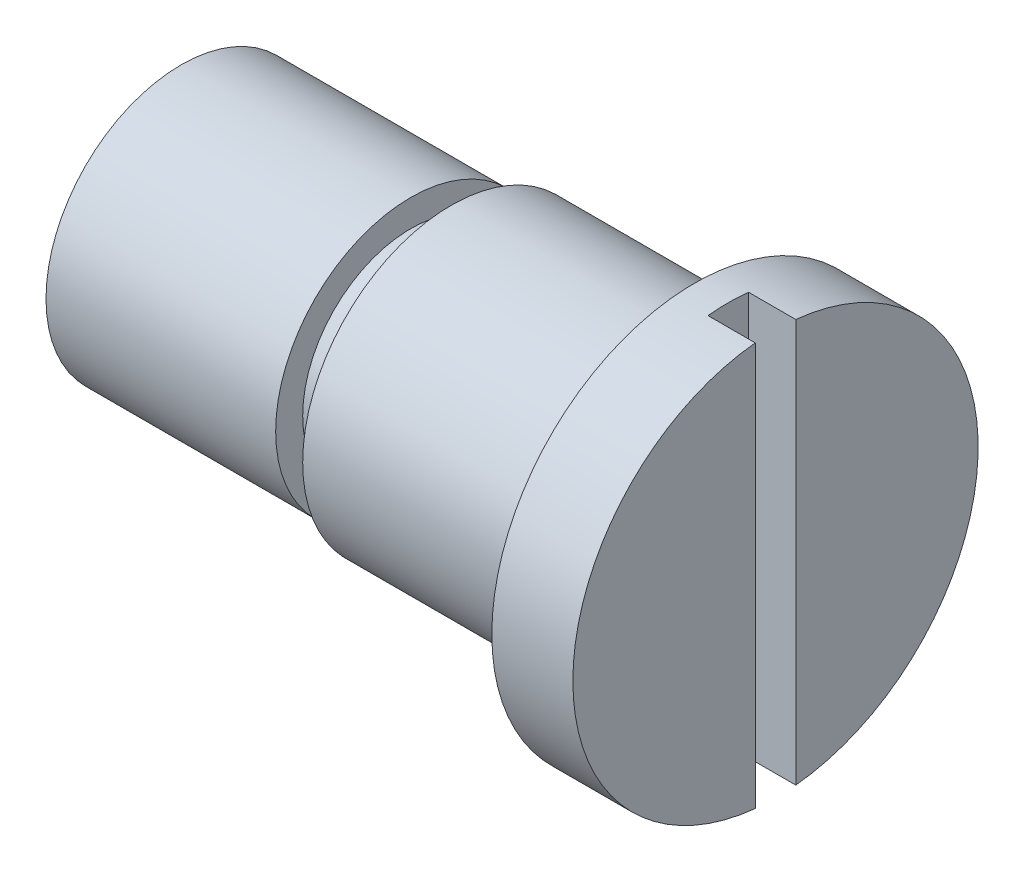
SolidWorks part; units mm, degrees
ref_plane "Front Plane" through (0, 0, 0) normal (0, 0, 1) x (1, 0, 0)
ref_plane "Top Plane" through (0, 0, 0) normal (0, 1, 0) x (1, 0, 0)
ref_plane "Right Plane" through (0, 0, 0) normal (1, 0, 0) x (0, 0, -1)
sketch "Sketch1" plane through (0, 0, 0) normal (0, 0, 1) x (1, 0, 0)
  line L0 (0, 0) -> (63.8199, 0) construction
  line L1 (0, 0) -> (0, 10)
  line L2 (0, 10) -> (17, 10)
  line L3 (17, 10) -> (17, 8)
  line L4 (17, 8) -> (20, 8)
  line L5 (20, 8) -> (20, 11)
  line L6 (20, 11) -> (38, 11)
  line L7 (38, 11) -> (38, 15)
  line L8 (38, 15) -> (44, 15)
  line L9 (44, 15) -> (44, 0)
  line L10 (0, 0) -> (44, 0)
  dimension "D6" = 6
  dimension "D1" = 10
  dimension "D2" = 17
  dimension "D3" = 8
  dimension "D4" = 3
  dimension "D5" = 11
  dimension "D7" = 15
  dimension "D8" = 38
revolve "Revolve1" add sketch "Sketch1" angle 360 about L0
sketch "Sketch2" plane through (44, 0, 0) normal (1, 0, 0) x (0, 0, -1)
  line L1 (-1.5, 16.9985) -> (1.5, 16.9985)
  line L2 (-1.5, 16.9985) -> (-1.5, -16.9985)
  line L3 (-1.5, -16.9985) -> (1.5, -16.9985)
  line L4 (1.5, 16.9985) -> (1.5, -16.9985)
  line L5 (0, -16.9985) -> (0, 16.9985) construction
  line L6 (-1.5, 0) -> (1.5, 0) construction
  point P0 (0, 0)
  dimension "D1" = 3
  dimension "D2" = 33.997
extrude "Cut-Extrude1" cut sketch "Sketch2" against normal blind 3.5
